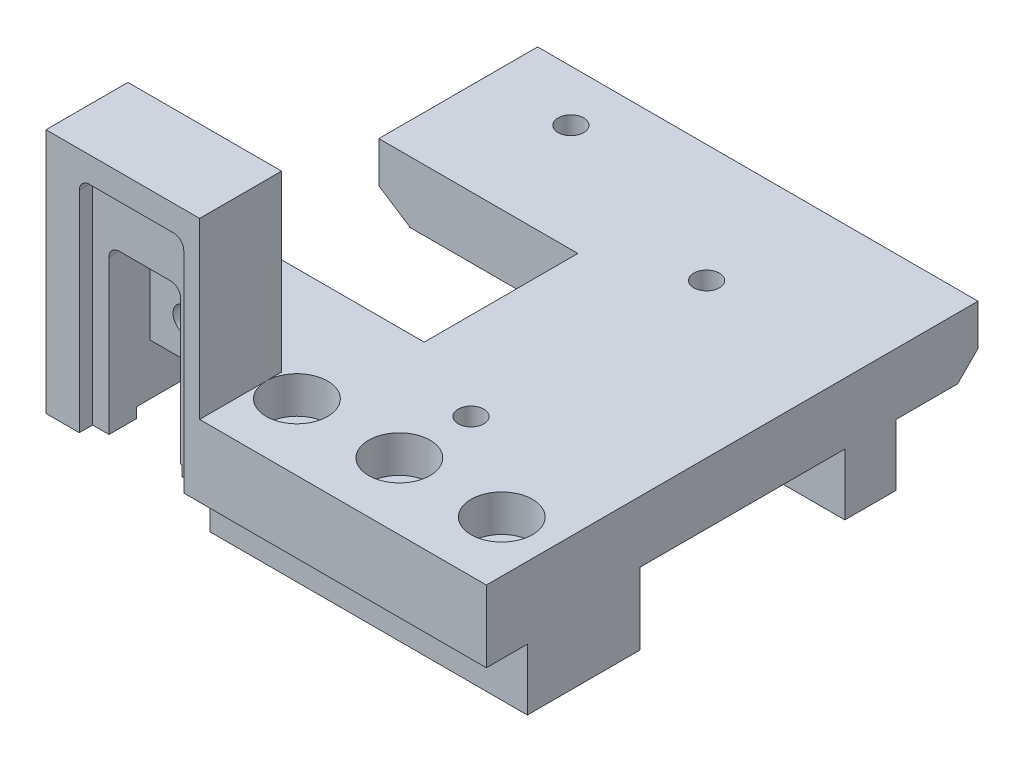
SolidWorks part; units mm, degrees
material "Ст 3 сп 5 ГОСТ 380-94"
ref_plane "Спереди" through (0, 0, 0) normal (0, 0, 1) x (1, 0, 0)
ref_plane "Сверху" through (0, 0, 0) normal (0, 1, 0) x (1, 0, 0)
ref_plane "Справа" through (0, 0, 0) normal (1, 0, 0) x (0, 0, -1)
sketch "Эскиз1" plane through (0, 0, 0) normal (0, 0, 1) x (1, 0, 0)
  line L1 (-25, 6.5) -> (25, 6.5)
  line L2 (-25, 6.5) -> (-25, -6.5)
  line L3 (-25, -6.5) -> (25, -6.5)
  line L4 (25, 6.5) -> (25, -6.5)
  line L5 (-25, 6.5) -> (25, -6.5) construction
  line L6 (-25, -6.5) -> (25, 6.5) construction
  point P0 (0, 0)
  dimension "D1" = 50
  dimension "D2" = 13
extrude "Бобышка-Вытянуть1" add sketch "Эскиз1" along normal blind 48
sketch "Эскиз2" plane through (-25, 0, 0) normal (-1, 0, 0) x (0, 0, 1)
  line L1 (48, -6.5) -> (44, -6.5)
  line L2 (48, -6.5) -> (48, -0.5)
  line L3 (48, -0.5) -> (44, -0.5)
  line L4 (44, -6.5) -> (44, -0.5)
  dimension "D1" = 4
  dimension "D2" = 6
sketch "Эскиз9" plane through (0, 6.5, 0) normal (0, 1, 0) x (1, 0, 0)
  line L0 (25, -48) -> (25, 0) construction
  line L1 (25, -48) -> (-25, -48) construction
  circle A0 centre (20, -41.5) radius 1.6
  circle A1 centre (10, -41.5) radius 1.6
  circle A2 centre (0, -41.5) radius 1.6
  dimension "D3" = 3.2
  dimension "D1" = 5
  dimension "D2" = 6.5
  dimension "D4" = 3
extrude "Вырез-Вытянуть7" cut sketch "Эскиз9" against normal through all
sketch "Эскиз10" plane through (0, 6.5, 0) normal (0, 1, 0) x (1, 0, 0)
  circle A0 centre (20, -41.5) radius 3
  circle A1 centre (10, -41.5) radius 3
  circle A2 centre (0, -41.5) radius 3
  dimension "D1" = 6
  dimension "D2" = 3
extrude "Вырез-Вытянуть10" cut sketch "Эскиз10" against normal blind 3.6
extrude "Вырез-Вытянуть15" cut sketch "Эскиз2" against normal through all
sketch "Эскиз18" plane through (-25, 0, 0) normal (-1, 0, 0) x (0, 0, 1)
  line L1 (33, 0.5) -> (13, 0.5)
  line L2 (33, 0.5) -> (33, -6.5)
  line L3 (33, -6.5) -> (13, -6.5)
  line L4 (13, 0.5) -> (13, -6.5)
  line L5 (44, -0.5) -> (44, -6.5) construction
  line L6 (48, 6.5) -> (0, 6.5) construction
  dimension "D1" = 6
  dimension "D2" = 20
  dimension "D3" = 11
extrude "Вырез-Вытянуть16" cut sketch "Эскиз18" against normal through all
sketch "Эскиз19" plane through (25, 0, 0) normal (1, 0, 0) x (0, 0, -1)
  line L0 (0, -6.5) -> (0, 6.5) construction
  line L1 (-13, -6.5) -> (0, -6.5)
  line L2 (-13, -6.5) -> (-13, -5.5)
  line L3 (-13, -5.5) -> (0, -5.5)
  line L4 (0, -6.5) -> (0, -5.5)
  dimension "D1" = 1
extrude "Вырез-Вытянуть17" cut sketch "Эскиз19" against normal through all
sketch "Эскиз21" plane through (25, 0, 0) normal (1, 0, 0) x (0, 0, -1)
  line L1 (0, -5.5) -> (-8, -5.5)
  line L2 (0, -5.5) -> (0, 0.5)
  line L3 (0, 0.5) -> (-8, 0.5)
  line L4 (-8, -5.5) -> (-8, 0.5)
  dimension "D1" = 6
  dimension "D2" = 8
extrude "Вырез-Вытянуть19" cut sketch "Эскиз21" against normal through all
chamfer "Фаска1" distance 2 angle 45 1 edges at (0, 0.5, 0)
sketch "Эскиз22" plane through (0, 0, 8) normal (0, 0, -1) x (-1, 0, 0)
  line L1 (25, 2.5) -> (15, 2.5)
  line L2 (25, 2.5) -> (25, -6.5)
  line L3 (25, -6.5) -> (15, -6.5)
  line L4 (15, 2.5) -> (15, -6.5)
  dimension "D1" = 10
extrude "Вырез-Вытянуть20" cut sketch "Эскиз22" against normal through all from offset 8
chamfer "Фаска2" distance 3 angle 33 1 edges at (-15, 2.5, 24)
sketch "Эскиз23" plane through (0, 0, 8) normal (0, 0, -1) x (-1, 0, 0)
  line L1 (15, 0.5) -> (6, 0.5)
  line L2 (15, 0.5) -> (15, -2)
  line L3 (15, -2) -> (6, -2)
  line L4 (6, 0.5) -> (6, -2)
  dimension "D1" = 2.5
  dimension "D2" = 9
extrude "Вырез-Вытянуть21" cut sketch "Эскиз23" against normal through all
sketch "Эскиз25" plane through (0, 0, 0) normal (0, 0, -1) x (-1, 0, 0)
  line L1 (26.8451, 6.8957) -> (20.964, 6.8957)
  line L2 (26.8451, 6.8957) -> (26.8451, 1.804)
  line L3 (26.8451, 1.804) -> (20.964, 1.804)
  line L4 (20.964, 6.8957) -> (20.964, 1.804)
sketch "Эскиз26" plane through (0, 0, 0) normal (0, 0, -1) x (-1, 0, 0)
  line L1 (25, 6.5) -> (18, 6.5)
  line L2 (25, 6.5) -> (25, 2.5)
  line L3 (25, 2.5) -> (18, 2.5)
  line L4 (18, 6.5) -> (18, 2.5)
extrude "Вырез-Вытянуть24" cut sketch "Эскиз26" against normal through all
sketch "Эскиз27" plane through (-18, 0, 0) normal (-1, 0, 0) x (0, 0, 1)
  line L1 (48, 6.5) -> (44, 6.5)
  line L2 (48, 6.5) -> (48, -0.5)
  line L3 (48, -0.5) -> (44, -0.5)
  line L4 (44, 6.5) -> (44, -0.5)
  dimension "D1" = 7
  dimension "D2" = 4
extrude "Бобышка-Вытянуть2" add sketch "Эскиз27" against normal blind 5
sketch "Эскиз35" [suppressed] plane through (0, 6.5, 0) normal (0, 1, 0) x (1, 0, 0)
  line L0 (-18, -48) -> (-18, 0) construction
  line L1 (-18, -15) -> (2, -15)
  line L2 (-18, -15) -> (-18, -30)
  line L3 (-18, -30) -> (2, -30)
  line L4 (2, -15) -> (2, -30)
  line L5 (25, 0) -> (-18, 0) construction
  dimension "D1" = 20
  dimension "D2" = 15
  dimension "D3" = 15
extrude "Вырез-Вытянуть28" [suppressed] cut sketch "Эскиз35" against normal through all
sketch "Эскиз36" [suppressed] plane through (0, 6.5, 0) normal (0, 1, 0) x (1, 0, 0)
  line L0 (-18, -15) -> (-18, 0) construction
  line L1 (25, 0) -> (-18, 0) construction
  circle A0 centre (-9.85, -4.5) radius 1.25
  dimension "D1" = 2.5
  dimension "D2" = 8.15
  dimension "D3" = 4.5
extrude "Вырез-Вытянуть29" [suppressed] cut sketch "Эскиз36" against normal blind 4.5
sketch "Эскиз37" plane through (0, 6.5, 0) normal (0, 1, 0) x (1, 0, 0)
  line L0 (25, -48) -> (25, 0) construction
  line L1 (25, -48) -> (-18, -48) construction
  circle A0 centre (10, -34.5) radius 1.25
  circle A1 centre (10, -11.5) radius 1.25
  dimension "D1" = 2.5
  dimension "D2" = 15
  dimension "D3" = 13.5
  dimension "D4" = 2
extrude "Вырез-Вытянуть30" cut sketch "Эскиз37" against normal blind 5
sketch "Эскиз38" plane through (0, 6.5, 0) normal (0, 1, 0) x (1, 0, 0)
  line L0 (-18, -48) -> (-18, 0) construction
  line L1 (-18, -40) -> (-3, -40)
  line L2 (-18, -40) -> (-18, -48)
  line L3 (-18, -48) -> (-3, -48)
  line L4 (-3, -40) -> (-3, -48)
  line L5 (25, -48) -> (-18, -48) construction
  dimension "D1" = 15
  dimension "D2" = 8
extrude "Бобышка-Вытянуть3" add sketch "Эскиз38" along normal blind 17
sketch "Эскиз39" plane through (0, 0, 48) normal (0, 0, 1) x (1, 0, 0)
  line L0 (-13, -0.5) -> (-18, -0.5) construction
  line L1 (-14.75, -0.5) -> (-4.55, -0.5)
  line L2 (-14.75, -0.5) -> (-14.75, 21)
  line L3 (-14.75, 21) -> (-4.55, 21)
  line L4 (-4.55, -0.5) -> (-4.55, 21)
  line L5 (-18, 23.5) -> (-18, -0.5) construction
  dimension "D1" = 3.25
  dimension "D2" = 10.2
  dimension "D3" = 21.5
extrude "Вырез-Вытянуть31" cut sketch "Эскиз39" against normal blind 1.3
fillet "Скругление2" radius 1 2 edges at (-14.75, 21, 47.35) (-4.55, 21, 47.35)
sketch "Эскиз40" plane through (0, 0, 46.7) normal (0, 0, 1) x (1, 0, 0)
  line L0 (-18, 23.5) -> (-3, 23.5) construction
  circle A0 centre (-9.65, 8.9) radius 1.25
  dimension "D1" = 2.5
  dimension "D2" = 14.6
extrude "Вырез-Вытянуть32" cut sketch "Эскиз40" against normal blind 6
sketch "Эскиз41" plane through (0, 0, 46.7) normal (0, 0, 1) x (1, 0, 0)
  line L1 (-13.15, -6.5) -> (-6.15, -6.5)
  line L2 (-13.15, -6.5) -> (-13.15, 15.5)
  line L3 (-13.15, 15.5) -> (-6.15, 15.5)
  line L4 (-6.15, -6.5) -> (-6.15, 15.5)
  line L6 (-14.75, 20) -> (-14.75, -0.5) construction
  line L8 (25, -6.5) -> (-15, -6.5) construction
  dimension "D1" = 1.6
  dimension "D2" = 7
  dimension "D3" = 22
extrude "Вырез-Вытянуть33" cut sketch "Эскиз41" against normal blind 4
sketch "Эскиз43" plane through (0, 0, 42.7) normal (0, 0, 1) x (1, 0, 0)
  line L1 (-13.15, -6.5) -> (-6.15, -6.5)
  line L2 (-13.15, -6.5) -> (-13.15, 5.5)
  line L3 (-13.15, 5.5) -> (-6.15, 5.5)
  line L4 (-6.15, -6.5) -> (-6.15, 5.5)
  dimension "D1" = 12
extrude "Вырез-Вытянуть35" cut sketch "Эскиз43" against normal blind 8
fillet "Скругление3" radius 1 2 edges at (-13.15, 15.5, 44.7) (-6.15, 15.5, 44.7)
sketch "Эскиз44" plane through (0, 6.5, 0) normal (0, 1, 0) x (1, 0, 0)
  line L0 (-18, -40) -> (-18, 0) construction
  line L1 (-18, -30.5) -> (1.4288, -30.5)
  line L2 (-18, -30.5) -> (-18, -15.5)
  line L3 (-18, -15.5) -> (1.4288, -15.5)
  line L4 (1.4288, -30.5) -> (1.4288, -15.5)
  line L5 (25, -48) -> (-3, -48) construction
  dimension "D1" = 17.5
  dimension "D2" = 15
extrude "Вырез-Вытянуть37" cut sketch "Эскиз44" against normal blind 8
sketch "Эскиз45" plane through (0, 6.5, 0) normal (0, 1, 0) x (1, 0, 0)
  line L0 (-18, -15.5) -> (-18, 0) construction
  line L1 (25, 0) -> (-18, 0) construction
  circle A0 centre (-9.75, -5) radius 1.25
  dimension "D1" = 2.5
  dimension "D2" = 8.25
  dimension "D3" = 5
extrude "Вырез-Вытянуть38" cut sketch "Эскиз45" against normal blind 5.5
sketch "Эскиз46" plane through (-15, 0, 0) normal (-1, 0, 0) x (0, 0, 1)
  line L1 (46.3988, -1.2965) -> (1.3109, -1.2965)
  line L2 (46.3988, -1.2965) -> (46.3988, -7.1018)
  line L3 (46.3988, -7.1018) -> (1.3109, -7.1018)
  line L4 (1.3109, -1.2965) -> (1.3109, -7.1018)
extrude "Вырез-Вытянуть39" cut sketch "Эскиз46" against normal blind 9
